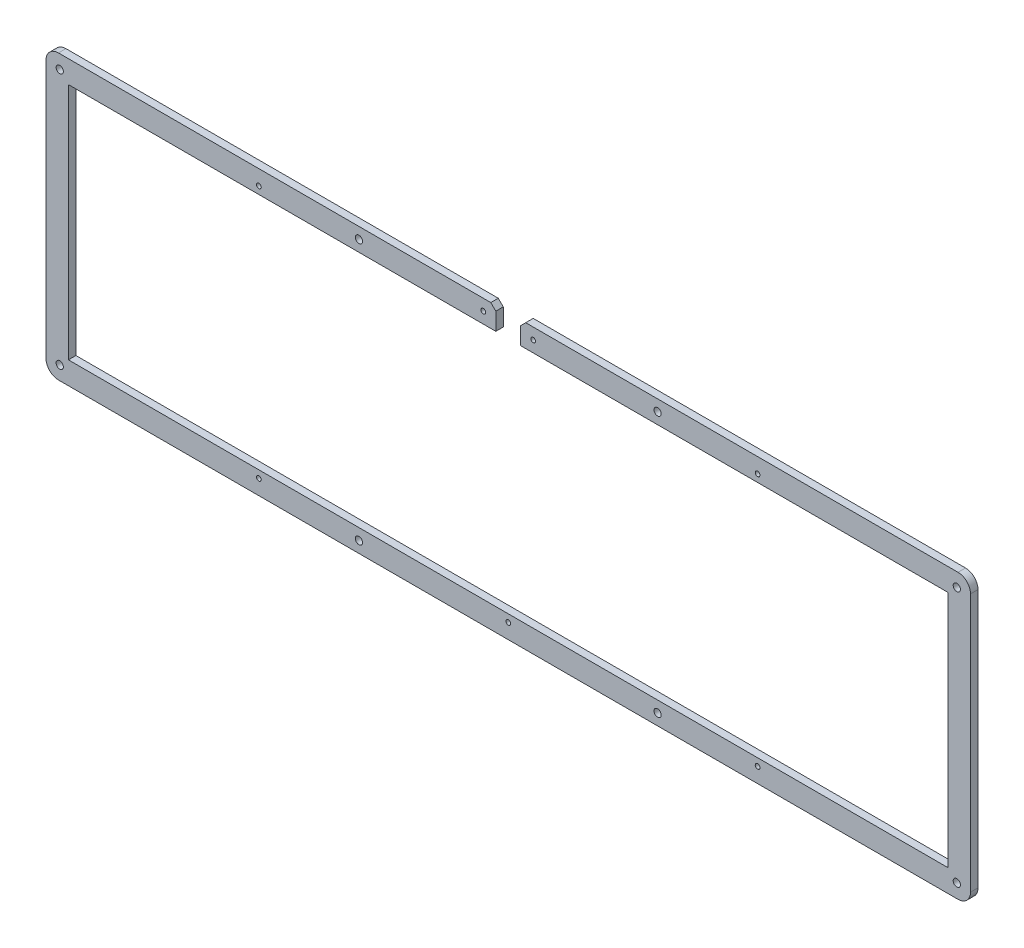
SolidWorks part; units mm, degrees
ref_plane "Front Plane" through (0, 0, 0) normal (0, 0, 1) x (1, 0, 0)
ref_plane "Top Plane" through (0, 0, 0) normal (0, 1, 0) x (1, 0, 0)
ref_plane "Right Plane" through (0, 0, 0) normal (1, 0, 0) x (0, 0, -1)
sketch "Model" plane through (0, 0, 0) normal (0, 0, 1) x (1, 0, 0)
  line L0 (0, 108.6) -> (0, 5)
  line L1 (9, 104.6) -> (9, 9)
  line L2 (365.775, 0) -> (5, 0)
  line L3 (361.775, 9) -> (9, 9)
  line L4 (370.775, 108.6) -> (370.775, 5)
  line L5 (361.775, 104.6) -> (361.775, 9)
  line L6 (180.3875, 104.6) -> (180.3875, 111.6)
  line L7 (180.3875, 111.6) -> (178.3875, 113.6)
  line L8 (190.3875, 111.6) -> (192.3875, 113.6)
  line L9 (190.3875, 104.6) -> (190.3875, 111.6)
  line L10 (9, 104.6) -> (180.3875, 104.6)
  line L11 (5, 113.6) -> (178.3875, 113.6)
  line L12 (190.3875, 104.6) -> (361.775, 104.6)
  line L13 (192.3875, 113.6) -> (365.775, 113.6)
  line L14 (5.5, 5.5) -> (5.5, 4.5)
  arc A0 (365.775, 0) -> (370.775, 5) centre (365.775, 5) ccw
  arc A1 (370.775, 108.6) -> (365.775, 113.6) centre (365.775, 108.6) ccw
  arc A2 (0, 5) -> (5, 0) centre (5, 5) ccw
  arc A3 (5, 113.6) -> (0, 108.6) centre (5, 108.6) ccw
  circle A4 centre (125.5, 4.5) radius 1.45
  circle A5 centre (195.3875, 109.1) radius 0.95
  circle A6 centre (175.3875, 109.1) radius 0.95
  circle A7 centre (5.5, 108.1) radius 1.45
  circle A8 centre (5.5, 5.5) radius 1.45
  circle A9 centre (365.275, 5.5) radius 1.45
  circle A10 centre (365.275, 108.1) radius 1.45
  circle A11 centre (85.3875, 107.6) radius 0.95
  circle A12 centre (285.3875, 107.6) radius 0.95
  circle A13 centre (85.3875, 6) radius 0.95
  circle A14 centre (185.3875, 6) radius 0.95
  circle A15 centre (285.3875, 6) radius 0.95
  circle A16 centre (245.275, 4.5) radius 1.45
  circle A17 centre (125.5, 109.1) radius 1.45
  circle A18 centre (245.275, 109.1) radius 1.45
  dimension "D6" = 1.9
  dimension "D7" = 1.9
  dimension "D9" = 1.9
  dimension "D8" = 1.9
  dimension "D10" = 1.9
  dimension "D11" = 1.9
  dimension "D12" = 1.9
  dimension "D13" = 2.9
  dimension "D1" = 352.775
  dimension "D2" = 370.775
  dimension "D3" = 95.6
  dimension "D4" = 113.6
  dimension "D5" = 113.6
extrude "Boss-Extrude1" add sketch "Model" along normal blind 3 contours L11 A3 L0 A2 L2 A0 L4 A1 L13 L8 L9 L12 L5 L3 L1 L10 L6 L7 A18 A17 A16 A15 A14 A13 A12 A11 A10 A9 A8 A7 A6 A5 A4
equation "\"A\"= 1.9mm"
equation "\"D6@Model\"=\"A\""
equation "\"D7@Model\"=\"A\""
equation "\"D9@Model\"=\"A\""
equation "\"D8@Model\"=\"A\""
equation "\"D10@Model\"=\"A\""
equation "\"D11@Model\"=\"A\""
equation "\"D12@Model\"=\"A\""
